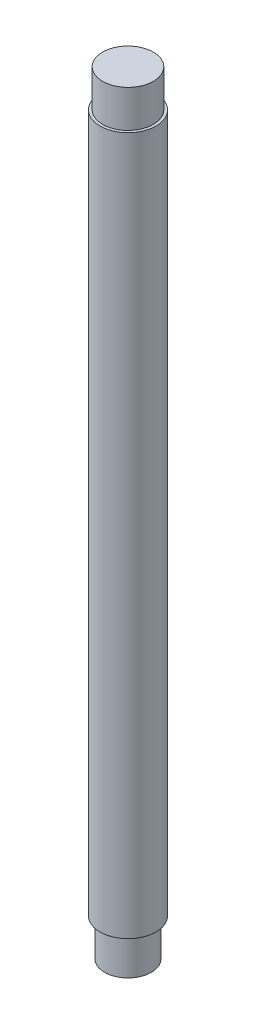
SolidWorks part; units mm, degrees
ref_plane "Front Plane" through (0, 0, 0) normal (0, 0, 1) x (1, 0, 0)
ref_plane "Top Plane" through (0, 0, 0) normal (0, 1, 0) x (1, 0, 0)
ref_plane "Right Plane" through (0, 0, 0) normal (1, 0, 0) x (0, 0, -1)
sketch "Sketch2" plane through (0, 0, 0) normal (0, 1, 0) x (1, 0, 0)
  circle A0 centre (0, 0) radius 9.525
  dimension "D1" = 19.05
extrude "Boss-Extrude1" add sketch "Sketch2" along normal blind 237.4
sketch "Sketch3" plane through (0, 237.4, 0) normal (0, 1, 0) x (1, 0, 0)
  circle A0 centre (0, 0) radius 8.621
extrude "Boss-Extrude2" add sketch "Sketch3" along normal blind 12.7
sketch "Sketch4" plane through (0, 0, 0) normal (0, -1, 0) x (1, 0, 0)
  circle A0 centre (0, 0) radius 7.9375
  dimension "D1" = 15.875
extrude "Boss-Extrude3" add sketch "Sketch4" along normal blind 12.7
